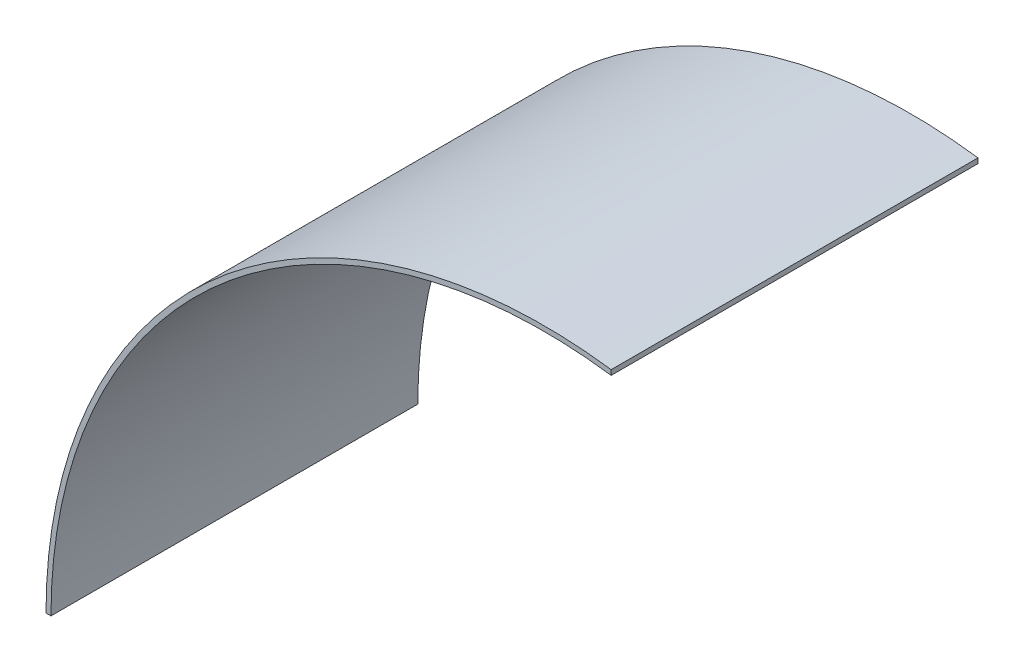
SolidWorks part; units mm, degrees
material "Plain Carbon Steel"
ref_plane "Front Plane" through (0, 0, 0) normal (0, 0, 1) x (1, 0, 0)
ref_plane "Top Plane" through (0, 0, 0) normal (0, 1, 0) x (1, 0, 0)
ref_plane "Right Plane" through (0, 0, 0) normal (1, 0, 0) x (0, 0, -1)
sketch "Sketch1" plane through (0, 0, 0) normal (0, 0, 1) x (1, 0, 0)
  line L0 (0, 0) -> (0, -152.4) construction
  line L2 (0, 0) -> (101.5936, 0) construction
  line L3 (20.5689, 113.7839) -> (20.5689, -22.985) construction
  line L5 (20.5689, 151.0056) -> (20.5689, 149.4725)
  line L7 (0, 0) -> (-150.8811, 0) construction
  line L10 (18.0689, 149.7952) -> (18.0689, 151.3251) construction
  line L25 (-152.4, 0) -> (-150.8811, 0)
  circle A0 centre (0, 0) radius 150.8811 construction
  circle A1 centre (0, 0) radius 152.4 construction
  arc A2 (-150.8811, 0) -> (20.5689, 149.4725) centre (0, 0) cw
  arc A3 (-152.4, 0) -> (20.5689, 151.0056) centre (0, 0) cw
  dimension "D1" = 301.7622
  dimension "D2" = 304.8
  dimension "D3" = 20.5689
  dimension "D4" = 5
extrude "Inner Ring - Left Side" add sketch "Sketch1" along normal blind 112.268
